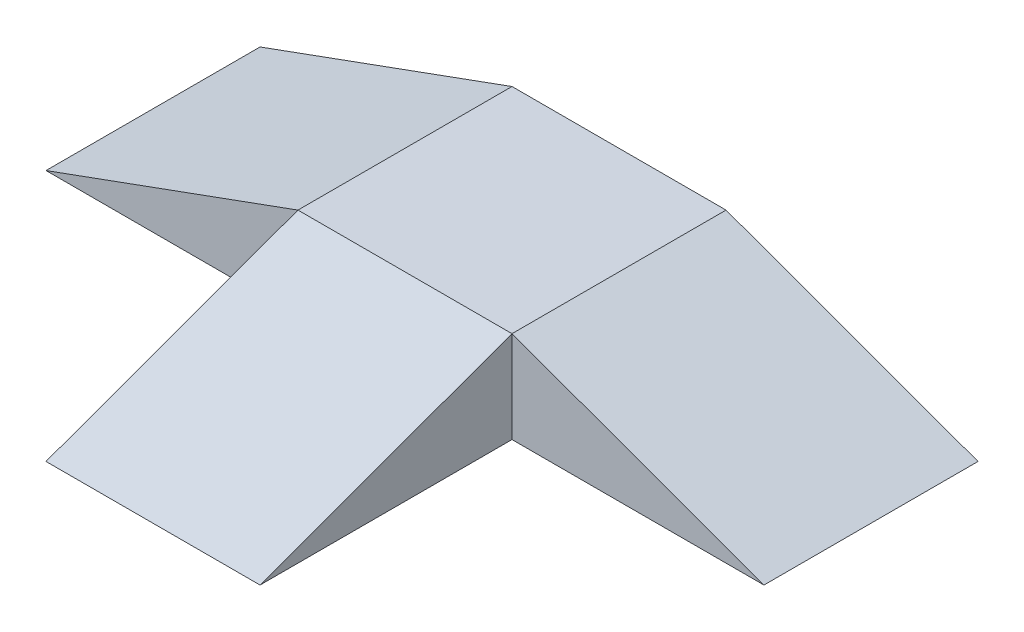
SolidWorks part; units mm, degrees
ref_plane "Front Plane" through (0, 0, 0) normal (0, 0, 1) x (1, 0, 0)
ref_plane "Top Plane" through (0, 0, 0) normal (0, 1, 0) x (1, 0, 0)
ref_plane "Right Plane" through (0, 0, 0) normal (1, 0, 0) x (0, 0, -1)
sketch "rampbase" plane through (0, 0, 0) normal (0, 1, 0) x (1, 0, 0)
  line L1 (-175, 175) -> (175, 175)
  line L2 (-175, 175) -> (-175, -175)
  line L3 (-175, -175) -> (175, -175)
  line L4 (175, 175) -> (175, -175)
  line L5 (-175, 175) -> (175, -175) construction
  line L6 (-175, -175) -> (175, 175) construction
  point P0 (0, 0)
  dimension "D1" = 350
  dimension "D2" = 350
extrude "Boss-Extrude1" add sketch "rampbase" along normal blind 150
sketch "Sketch6" plane through (175, 0, 0) normal (1, 0, 0) x (0, 0, -1)
  line L0 (-175, 150) -> (-175, 0)
  line L1 (-175, 0) -> (-587, 0)
  line L2 (-587, 0) -> (-175, 150)
  dimension "D1" = 412
extrude "Boss-Extrude3" add sketch "Sketch6" against normal blind 350
sketch "Sketch7" plane through (0, 0, -175) normal (0, 0, -1) x (-1, 0, 0)
  line L0 (0, 0) -> (0, 150) construction
  line L1 (-175, 0) -> (175, 0) construction
  line L2 (-175, 150) -> (175, 150) construction
  line L3 (175, 150) -> (175, 0)
  line L4 (175, 0) -> (587, 0)
  line L5 (587, 0) -> (175, 150)
  line L6 (-175, 0) -> (-587, 0)
  line L7 (-175, 150) -> (-175, 0)
  line L8 (-587, 0) -> (-175, 150)
  dimension "D1" = 412
extrude "Boss-Extrude5" add sketch "Sketch7" against normal blind 350
